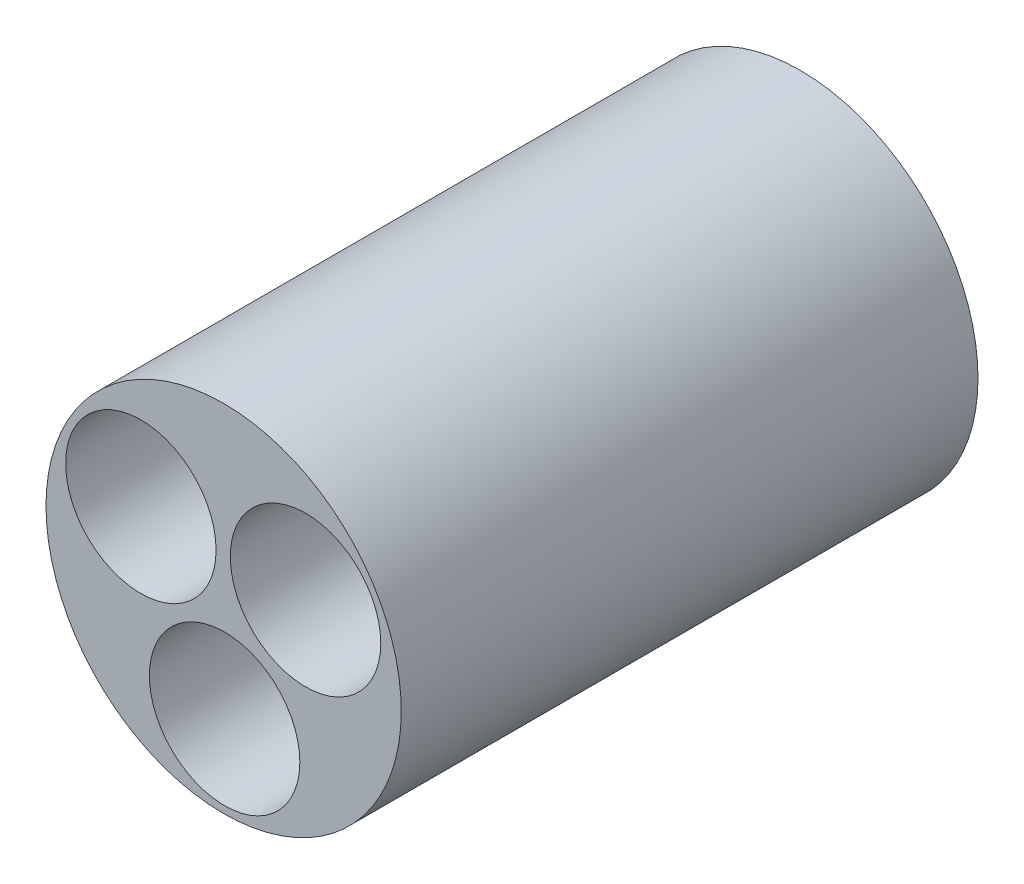
SolidWorks part; units mm, degrees
ref_plane "Front Plane" through (0, 0, 0) normal (0, 0, 1) x (1, 0, 0)
ref_plane "Top Plane" through (0, 0, 0) normal (0, 1, 0) x (1, 0, 0)
ref_plane "Right Plane" through (0, 0, 0) normal (1, 0, 0) x (0, 0, -1)
sketch "Sketch1" plane through (0, 0, 0) normal (0, 0, 1) x (1, 0, 0)
  line L0 (0, 0) -> (-20.1218, 11.3741) construction
  line L1 (0, 0) -> (19.9112, 11.7389) construction
  line L2 (0, 0) -> (0.2377, -23.114) construction
  circle A4 centre (0.1189, -11.557) radius 9.144
  circle A5 centre (9.9556, 5.8695) radius 9.144
  circle A6 centre (-10.0609, 5.687) radius 9.144
  circle A8 centre (0, 0) radius 21.59
  point P1 (2.188, 1.29)
  point P2 (-2.2112, 1.2499)
  point P6 (0.0261, -2.54)
  point P7 (9.9556, 5.8695)
  point P8 (-10.0609, 5.687)
  point P9 (0.1189, -11.557)
  dimension "D1" = 2.54
  dimension "D2" = 2.54
  dimension "D3" = 2.54
  dimension "D4" = 9.017
  dimension "D5" = 9.017
  dimension "D6" = 9.017
extrude "Boss-Extrude1" add sketch "Sketch1" along normal blind 70.1
